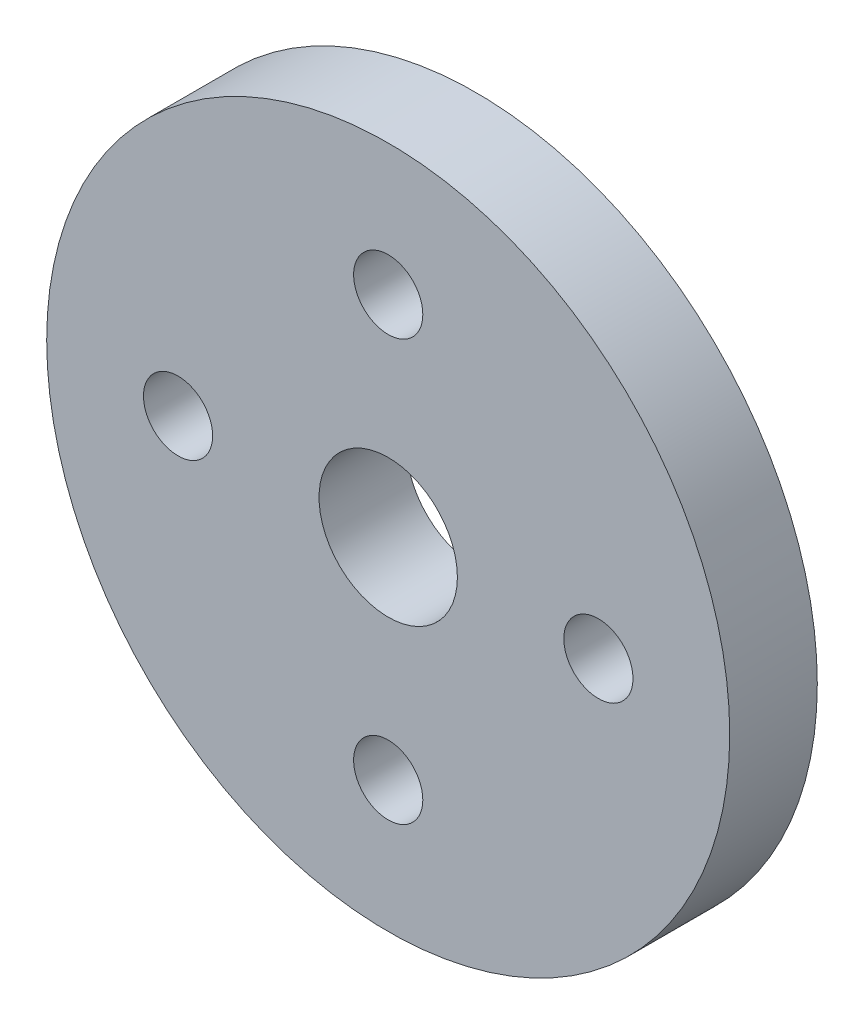
SolidWorks part; units mm, degrees
ref_plane "Front Plane" through (0, 0, 0) normal (0, 0, 1) x (1, 0, 0)
ref_plane "Top Plane" through (0, 0, 0) normal (0, 1, 0) x (1, 0, 0)
ref_plane "Right Plane" through (0, 0, 0) normal (1, 0, 0) x (0, 0, -1)
sketch "Sketch1" plane through (0, 0, 0) normal (0, 0, 1) x (1, 0, 0)
  line L0 (0, 0) -> (0, 19.5) construction
  line L1 (0, 0) -> (-19.5, 0) construction
  circle A0 centre (0, 0) radius 19.5
  circle A1 centre (0, 0) radius 3.95
  circle A2 centre (0, 12) radius 1.975
  circle A3 centre (12, 0) radius 1.975
  circle A4 centre (0, -12) radius 1.975
  circle A5 centre (-12, 0) radius 1.975
  point P17 (0, 0)
  dimension "D1" = 39
  dimension "D2" = 7.9
  dimension "D3" = 3.95
  dimension "D4" = 12
  dimension "D5" = 4
extrude "Boss-Extrude1" add sketch "Sketch1" along normal blind 5
